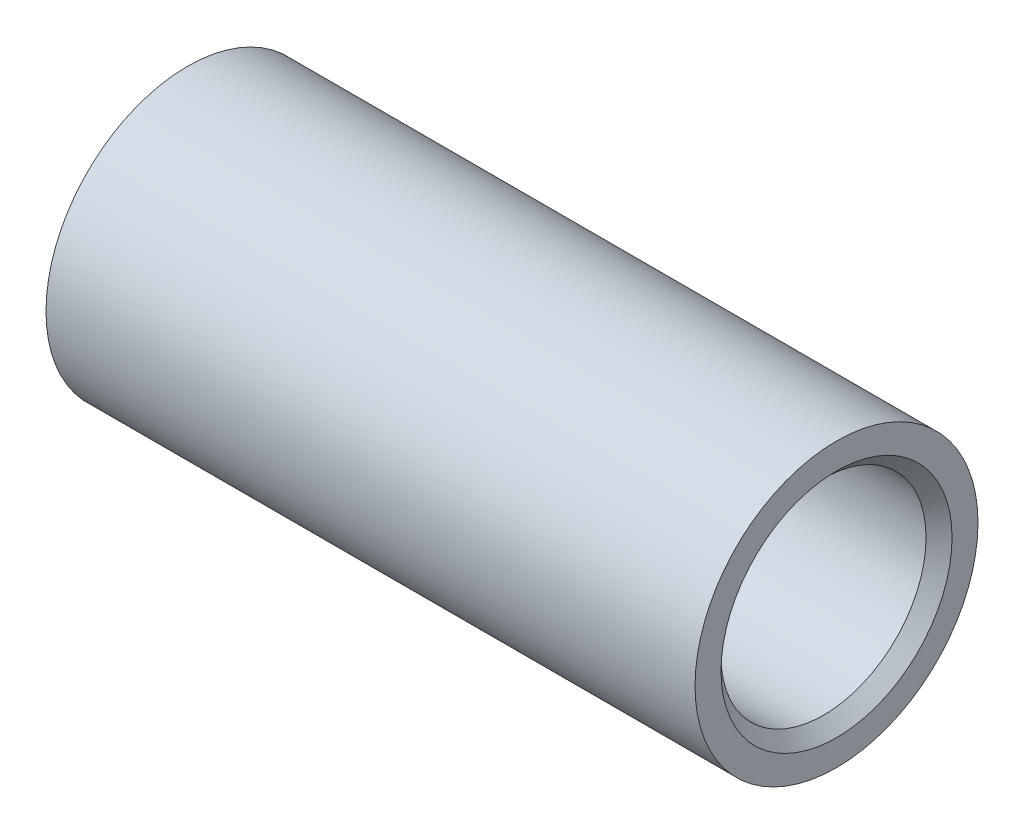
SolidWorks part; units mm, degrees
material "PE Low/Medium Density"
ref_plane "Front Plane" through (0, 0, 0) normal (0, 0, 1) x (1, 0, 0)
ref_plane "Top Plane" through (0, 0, 0) normal (0, 1, 0) x (1, 0, 0)
ref_plane "Right Plane" through (0, 0, 0) normal (1, 0, 0) x (0, 0, -1)
sketch "Sketch1" plane through (0, 0, 0) normal (0, 0, 1) x (1, 0, 0)
  line L0 (-4.5618, 0) -> (12.7, 0) construction
  line L1 (0, 2.7686) -> (12.7, 2.7686)
  line L2 (12.7, 2.7686) -> (12.7, 2.0066)
  line L3 (12.7, 2.0066) -> (4.3434, 2.0066)
  line L4 (0, 2.7686) -> (0, 2.0066)
  line L5 (0, 2.0066) -> (3.8354, 2.0066)
  line L6 (4.4842, 0.381) -> (4.9922, 0.381)
  arc A0 (4.3434, 2.0066) -> (4.9922, 0.381) centre (2.4532, 0.31) cw
  arc A1 (3.8354, 2.0066) -> (4.4842, 0.381) centre (1.9452, 0.31) cw
  dimension "D6" = 2.54
  dimension "D7" = 2.54
  dimension "D9" = 0.762
  dimension "D1" = 12.7
  dimension "D2" = 0.762
  dimension "D3" = 8.3566
  dimension "D4" = 0.508
  dimension "D5" = 0.508
  dimension "D8" = 4.0132
revolve "Revolve1" add sketch "Sketch1" angle 360 about L0
chamfer "Chamfer1" distance 0.254 angle 45 1 edges at (12.7, 0, 2.0066)
